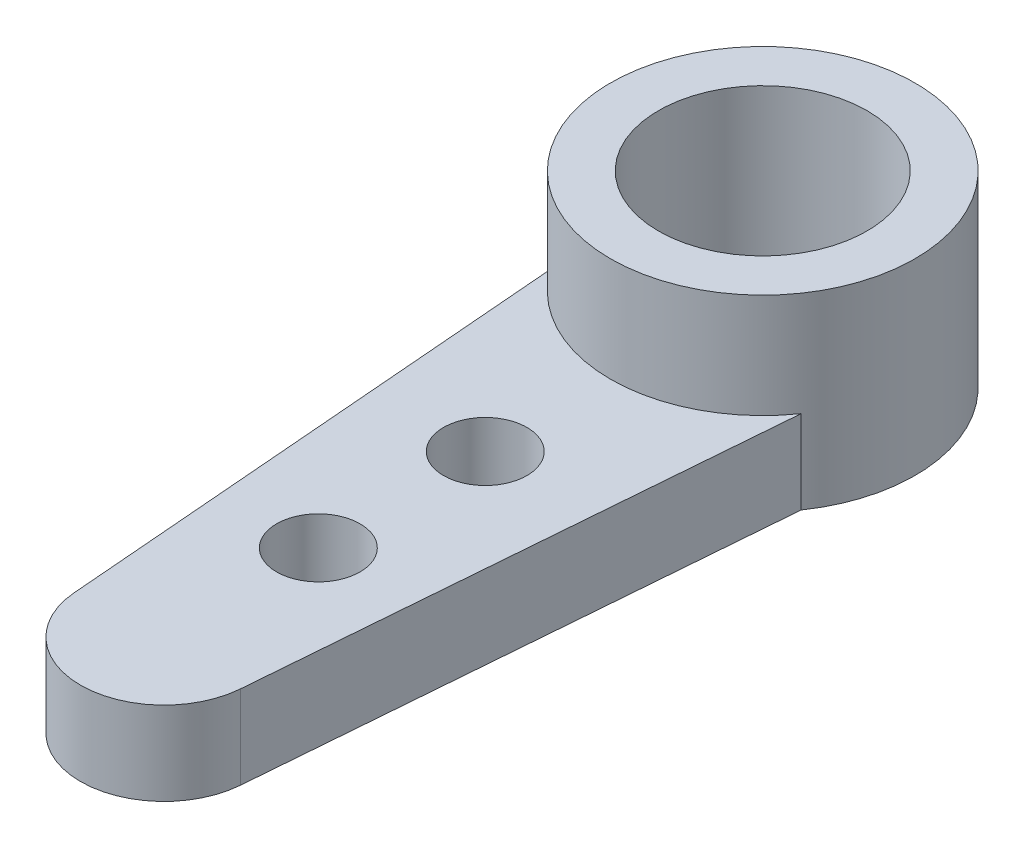
SolidWorks part; units mm, degrees
ref_plane "Front Plane" through (0, 0, 0) normal (0, 0, 1) x (1, 0, 0)
ref_plane "Top Plane" through (0, 0, 0) normal (0, 1, 0) x (1, 0, 0)
ref_plane "Right Plane" through (0, 0, 0) normal (1, 0, 0) x (0, 0, -1)
sketch "Sketch1" plane through (0, 0, 0) normal (0, 1, 0) x (1, 0, 0)
  line L0 (3, -2.0791) -> (1.9935, -14.5114)
  line L1 (-1.9935, -14.5114) -> (-3, -2.0791)
  arc A0 (3, -2.0791) -> (-3, -2.0791) centre (0, 0) ccw
  arc A1 (1.9935, -14.5114) -> (-1.9935, -14.5114) centre (0, -14.35) cw
  circle A2 centre (0, -6.65) radius 1
  circle A3 centre (0, -10.65) radius 1
  circle A4 centre (0, 0) radius 2.5
  dimension "D1" = 7.3
  dimension "D2" = 20
  dimension "D4" = 2
  dimension "D5" = 2
  dimension "D6" = 2
  dimension "D7" = 3
  dimension "D8" = 7
  dimension "D9" = 5
  dimension "D3" = 6
extrude "Boss-Extrude1" add sketch "Sketch1" along normal blind 2
sketch "Sketch2" plane through (0, 2, 0) normal (0, 1, 0) x (1, 0, 0)
  circle A0 centre (0, 0) radius 3.65
  circle A1 centre (0, 0) radius 2.5
extrude "Boss-Extrude2" add sketch "Sketch2" along normal blind 2.5
